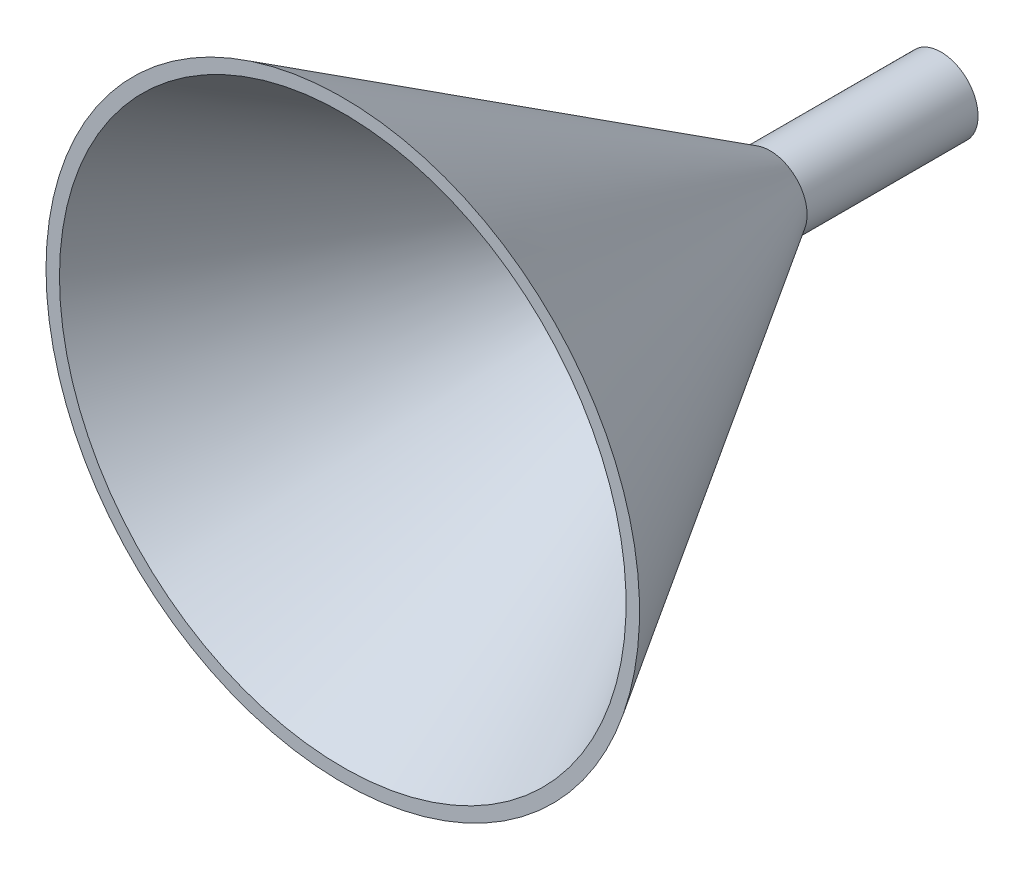
SolidWorks part; units mm, degrees
ref_plane "Front Plane" through (0, 0, 0) normal (0, 0, 1) x (1, 0, 0)
ref_plane "Top Plane" through (0, 0, 0) normal (0, 1, 0) x (1, 0, 0)
ref_plane "Right Plane" through (0, 0, 0) normal (1, 0, 0) x (0, 0, -1)
sketch "Sketch1" plane through (0, 0, 0) normal (0, 1, 0) x (1, 0, 0)
  line L0 (0, 0) -> (0, -25.4)
  line L1 (0, 0) -> (1.5, 0)
  line L2 (1.5, 0) -> (1.5, -25.4)
  line L3 (1.5, -25.4) -> (40.1, -88.9)
  line L5 (-4, 0) -> (-4, -25.4) construction
  line L6 (40.1, -88.9) -> (38.1, -88.9)
  line L7 (38.1, -88.9) -> (0, -25.4)
  dimension "D1" = 1.5
  dimension "D2" = 38.1
  dimension "D3" = 25.4
  dimension "D4" = 2
  dimension "D5" = 4
  dimension "D6" = 63.5
revolve "Revolve1" add sketch "Sketch1" angle 360 about L5
